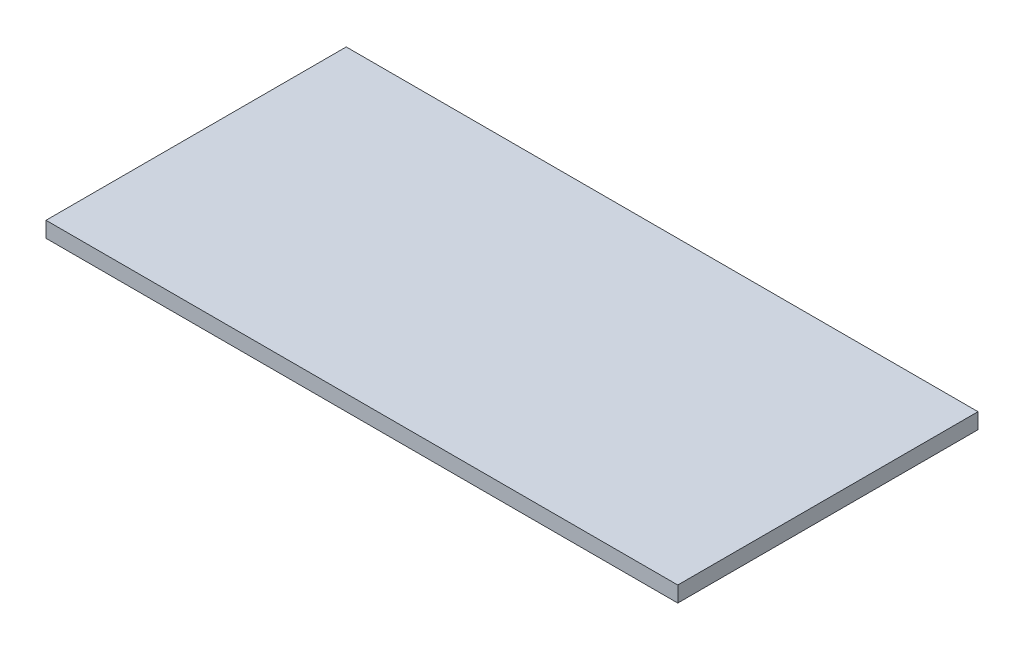
SolidWorks part; units mm, degrees
ref_plane "Front Plane" through (0, 0, 0) normal (0, 0, 1) x (1, 0, 0)
ref_plane "Top Plane" through (0, 0, 0) normal (0, 1, 0) x (1, 0, 0)
ref_plane "Right Plane" through (0, 0, 0) normal (1, 0, 0) x (0, 0, -1)
sketch "Sketch1" plane through (0, 0, 0) normal (0, 1, 0) x (1, 0, 0)
  line L1 (0, 0) -> (121.0056, 0)
  line L2 (0, 0) -> (0, -57.5056)
  line L3 (0, -57.5056) -> (121.0056, -57.5056)
  line L4 (121.0056, 0) -> (121.0056, -57.5056)
  dimension "D1" = 121.0056
  dimension "D2" = 57.5056
extrude "Boss-Extrude1" add sketch "Sketch1" along normal blind 2.9972
